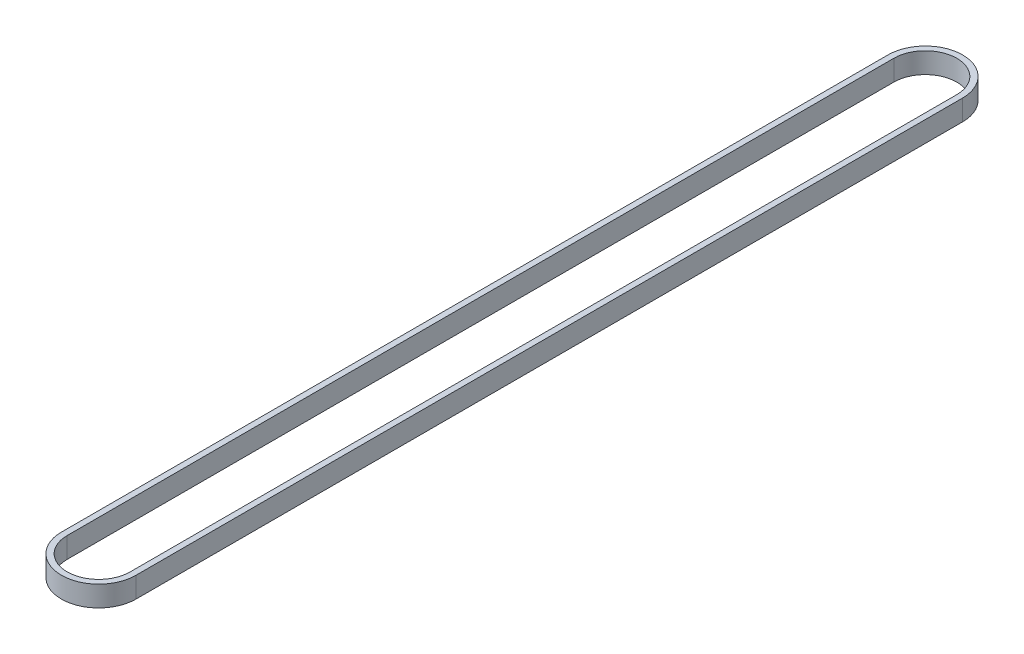
SolidWorks part; units mm, degrees
ref_plane "Front Plane" through (0, 0, 0) normal (0, 0, 1) x (1, 0, 0)
ref_plane "Top Plane" through (0, 0, 0) normal (0, 1, 0) x (1, 0, 0)
ref_plane "Right Plane" through (0, 0, 0) normal (1, 0, 0) x (0, 0, -1)
sketch "Sketch1" plane through (0, 0, 0) normal (0, 1, 0) x (1, 0, 0)
  line L0 (-13.716, 360) -> (-13.716, 0)
  line L1 (13.716, 360) -> (13.716, 0)
  line L2 (0, 360) -> (0, 0) construction
  line L3 (-16.256, 360) -> (-16.256, 0)
  line L4 (16.256, 360) -> (16.256, 0)
  arc A0 (-13.716, 0) -> (13.716, 0) centre (0, 0) ccw
  arc A1 (13.716, 360) -> (-13.716, 360) centre (0, 360) ccw
  arc A2 (16.256, 360) -> (-16.256, 360) centre (0, 360) ccw
  arc A3 (-16.256, 0) -> (16.256, 0) centre (0, 0) ccw
  dimension "D2" = 27.432
  dimension "D1" = 360
  dimension "D3" = 2.54
extrude "Boss-Extrude1" add sketch "Sketch1" along normal blind 9
